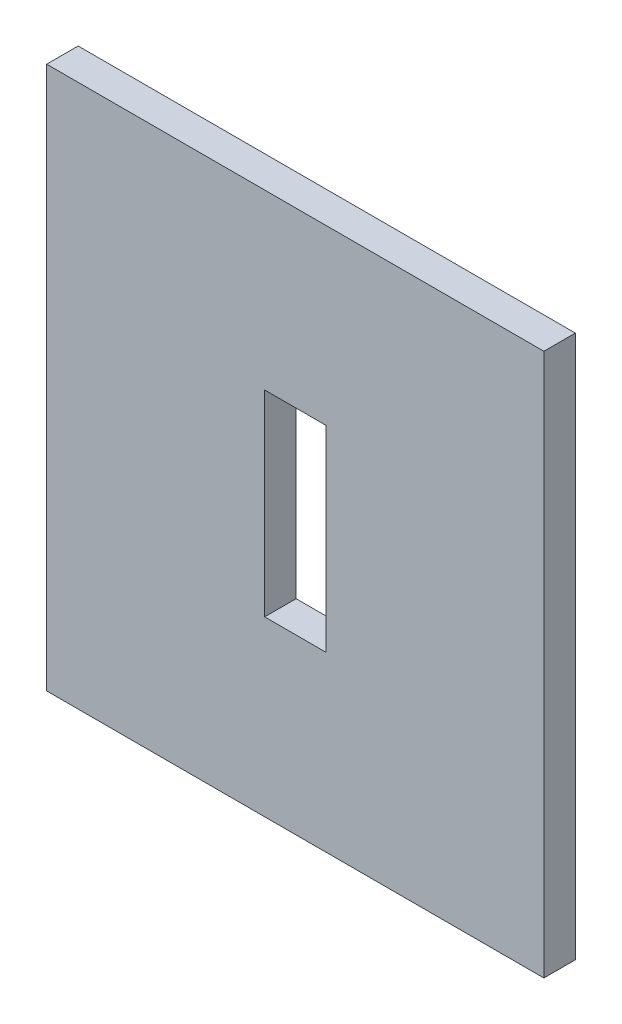
SolidWorks part; units mm, degrees
material "Maple"
ref_plane "Front Plane" through (0, 0, 0) normal (0, 0, 1) x (1, 0, 0)
ref_plane "Top Plane" through (0, 0, 0) normal (0, 1, 0) x (1, 0, 0)
ref_plane "Right Plane" through (0, 0, 0) normal (1, 0, 0) x (0, 0, -1)
sketch "Sketch1" plane through (0, 0, 0) normal (0, 0, 1) x (1, 0, 0)
  line L1 (-25.085, 27.385) -> (25.085, 27.385)
  line L2 (-25.085, 27.385) -> (-25.085, -27.385)
  line L3 (-25.085, -27.385) -> (25.085, -27.385)
  line L4 (25.085, 27.385) -> (25.085, -27.385)
  line L5 (-25.085, 27.385) -> (25.085, -27.385) construction
  line L6 (-25.085, -27.385) -> (25.085, 27.385) construction
  point P0 (0, 0)
  dimension "D1" = 50.17
  dimension "D2" = 54.77
extrude "Boss-Extrude1" add sketch "Sketch1" along normal blind 3.175
sketch "Sketch3" plane through (0, 0, 3.175) normal (0, 0, 1) x (1, 0, 0)
  line L1 (3.09, 9.915) -> (-3.09, 9.915)
  line L2 (3.09, 9.915) -> (3.09, -9.915)
  line L3 (3.09, -9.915) -> (-3.09, -9.915)
  line L4 (-3.09, 9.915) -> (-3.09, -9.915)
  line L5 (3.09, 9.915) -> (-3.09, -9.915) construction
  line L6 (3.09, -9.915) -> (-3.09, 9.915) construction
  point P0 (0, 0)
  dimension "D1" = 19.83
  dimension "D2" = 6.18
extrude "Cut-Extrude2" cut sketch "Sketch3" against normal through all
equation "\"length\"=50"
equation "\"D1@Sketch1\"=\"length\" + 2*\"kerf\""
equation "\"width\"=54.6"
equation "\"D2@Sketch1\"=\"width\" + 2*\"kerf\""
equation "\"depth\"=3.175"
equation "\"D1@Boss-Extrude1\"=\"depth\""
equation "\"width2\"=20"
equation "\"D1@Sketch3\"=\"width2\" - 2*\"kerf\""
equation "\"dist\"=6.35"
equation "\"D2@Sketch3\"=\"dist\" - 2*\"kerf\""
equation "\"kerf\"= 0.17 / 2"
